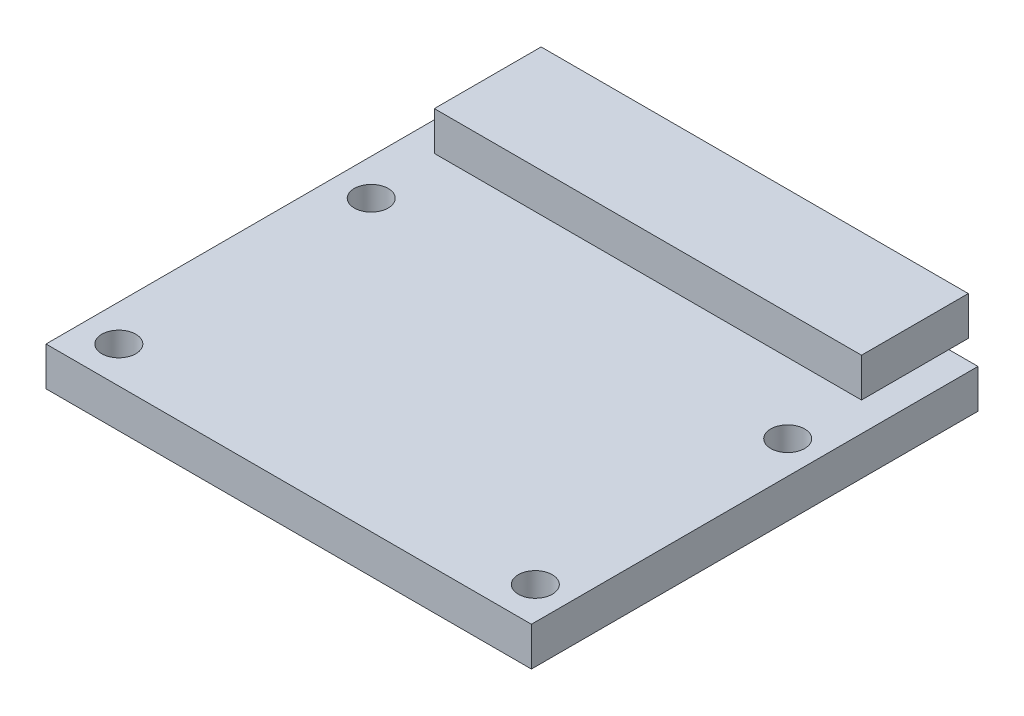
SolidWorks part; units mm, degrees
ref_plane "Alzado" through (0, 0, 0) normal (0, 0, 1) x (1, 0, 0)
ref_plane "Planta" through (0, 0, 0) normal (0, 1, 0) x (1, 0, 0)
ref_plane "Vista lateral" through (0, 0, 0) normal (1, 0, 0) x (0, 0, -1)
sketch "Croquis1" plane through (0, 0, 0) normal (0, 1, 0) x (1, 0, 0)
  line L1 (-12.5, -11.5) -> (12.5, -11.5)
  line L2 (-12.5, -11.5) -> (-12.5, 11.5)
  line L3 (-12.5, 11.5) -> (12.5, 11.5)
  line L4 (12.5, -11.5) -> (12.5, 11.5)
  line L5 (-12.5, -11.5) -> (12.5, 11.5) construction
  line L6 (-12.5, 11.5) -> (12.5, -11.5) construction
  point P0 (0, 0)
  dimension "D1" = 25
  dimension "D2" = 23
extrude "Saliente-Extruir1" add sketch "Croquis1" along normal blind 2
sketch "Croquis2" plane through (0, 0, 0) normal (0, -1, 0) x (1, 0, 0)
  line L1 (12.5, -11.5) -> (-12.5, -11.5) construction
  line L2 (-4.25, -6) -> (4.25, -6)
  line L3 (-4.25, -6) -> (-4.25, 2.5)
  line L4 (-4.25, 2.5) -> (4.25, 2.5)
  line L5 (4.25, -6) -> (4.25, 2.5)
  line L6 (-4.25, -6) -> (4.25, 2.5) construction
  line L7 (-4.25, 2.5) -> (4.25, -6) construction
  point P2 (0, -1.75)
  point P7 (0, 0)
  dimension "D1" = 8.5
  dimension "D2" = 8.5
  dimension "D3" = 5.5
extrude "Saliente-Extruir2" add sketch "Croquis2" along normal blind 3
sketch "Croquis3" plane through (0, -3, 0) normal (0, -1, 0) x (1, 0, 0)
  circle A0 centre (0, -1.75) radius 3.75
  dimension "D1" = 7.5
extrude "Saliente-Extruir3" add sketch "Croquis3" along normal blind 3
sketch "Croquis4" plane through (0, 0, 0) normal (0, -1, 0) x (1, 0, 0)
  line L0 (-12.5, -11.5) -> (-12.5, 11.5) construction
  line L1 (12.5, 11.5) -> (12.5, -11.5) construction
  line L2 (-12.5, 11.5) -> (12.5, 11.5) construction
  circle A0 centre (-10.625, 9.625) radius 0.875
  circle A1 centre (10.825, 9.625) radius 0.875
  circle A2 centre (10.825, -3.375) radius 0.875
  circle A3 centre (-10.625, -3.375) radius 0.875
  point P8 (0, 0)
  point P9 (0, 0)
  point P10 (0, 0)
  point P11 (0, 0)
  dimension "D1" = 1.75
  dimension "D2" = 1.875
  dimension "D3" = 1.675
  dimension "D4" = 1.875
  dimension "D5" = 13
extrude "Cortar-Extruir1" cut sketch "Croquis4" against normal blind 3
sketch "Croquis5" plane through (0, 2, 0) normal (0, 1, 0) x (1, 0, 0)
  line L1 (-11, 7) -> (11, 7)
  line L2 (-11, 7) -> (-11, 12.5)
  line L3 (-11, 12.5) -> (11, 12.5)
  line L4 (11, 7) -> (11, 12.5)
  line L5 (-11, 7) -> (11, 12.5) construction
  line L6 (-11, 12.5) -> (11, 7) construction
  line L7 (-12.5, -11.5) -> (12.5, -11.5) construction
  point P0 (0, 9.75)
  point P5 (0, 0)
  dimension "D1" = 5.5
  dimension "D2" = 22
  dimension "D3" = 18.5
extrude "Saliente-Extruir4" add sketch "Croquis5" along normal blind 2
